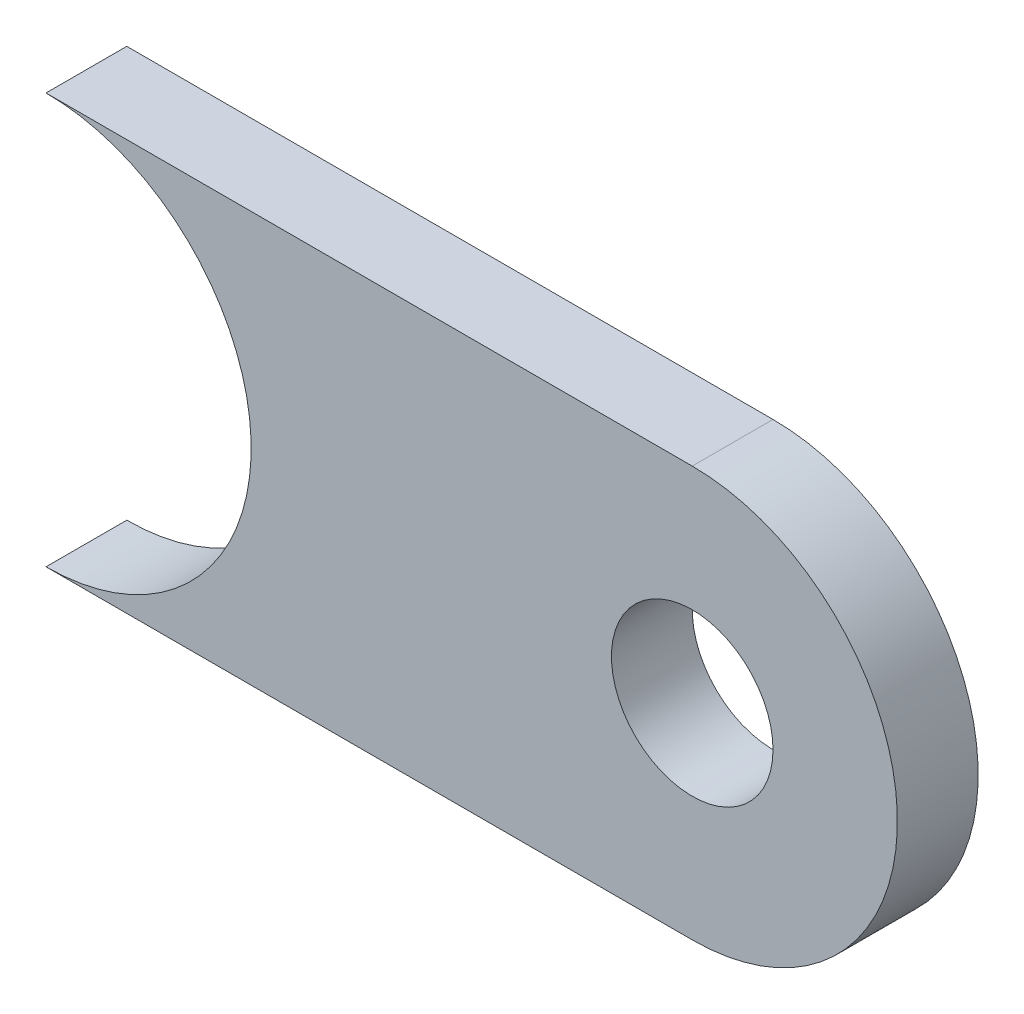
SolidWorks part; units mm, degrees
ref_plane "Front Plane" through (0, 0, 0) normal (0, 0, 1) x (1, 0, 0)
ref_plane "Top Plane" through (0, 0, 0) normal (0, 1, 0) x (1, 0, 0)
ref_plane "Right Plane" through (0, 0, 0) normal (1, 0, 0) x (0, 0, -1)
sketch "Sketch2" plane through (0, 0, 0) normal (0, 0, 1) x (1, 0, 0)
  line L1 (0, 12.7) -> (40, 12.7)
  line L3 (0, -12.7) -> (40, -12.7)
  arc A0 (0, -12.7) -> (0, 12.7) centre (0, 0) ccw
  arc A1 (40, -12.7) -> (40, 12.7) centre (40, 0) ccw
  circle A2 centre (40, 0) radius 5
  point P8 (0, 0)
  point P9 (0, 0)
  dimension "D1" = 25.4
  dimension "D3" = 10
  dimension "D4" = 12.7
  dimension "D5" = 25.4
  dimension "D2" = 40
extrude "Boss-Extrude2" add sketch "Sketch2" along normal blind 5
